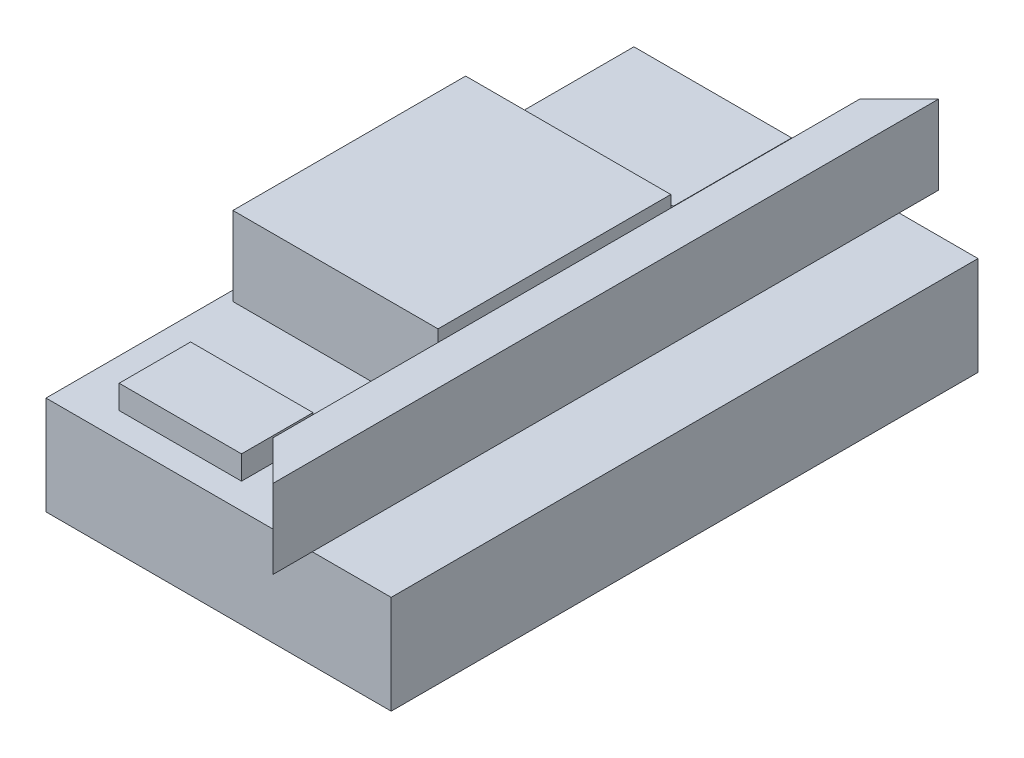
SolidWorks part; units mm, degrees
ref_plane "Front Plane" through (0, 0, 0) normal (0, 0, 1) x (1, 0, 0)
ref_plane "Top Plane" through (0, 0, 0) normal (0, 1, 0) x (1, 0, 0)
ref_plane "Right Plane" through (0, 0, 0) normal (1, 0, 0) x (0, 0, -1)
sketch "Sketch1" plane through (0, 0, 0) normal (0, 0, 1) x (1, 0, 0)
  line L1 (0, 0) -> (222.25, 0)
  line L2 (0, 0) -> (0, 63.5)
  line L3 (0, 63.5) -> (222.25, 63.5)
  line L4 (222.25, 0) -> (222.25, 63.5)
  dimension "D1" = 63.5
  dimension "D2" = 222.25
extrude "Boss-Extrude1" add sketch "Sketch1" along normal blind 377.825
sketch "Sketch2" plane through (0, 63.5, 0) normal (0, 1, 0) x (1, 0, 0)
  line L0 (222.25, -377.825) -> (222.25, 0) construction
  line L1 (171.45, -403.225) -> (146.05, -403.225)
  line L2 (171.45, -403.225) -> (171.45, 25.4)
  line L3 (171.45, 25.4) -> (146.05, 25.4)
  line L4 (146.05, -403.225) -> (146.05, 25.4)
  line L7 (222.25, -377.825) -> (0, -377.825) construction
  line L8 (222.25, 0) -> (0, 0) construction
  dimension "D1" = 25.4
  dimension "D2" = 50.8
  dimension "D3" = 25.4
  dimension "D4" = 25.4
extrude "Boss-Extrude2" add sketch "Sketch2" along normal blind 50.8
sketch "Sketch3" plane through (0, 63.5, 0) normal (0, 1, 0) x (1, 0, 0)
  line L0 (0, -377.825) -> (0, 0) construction
  line L1 (138.43, -113.9825) -> (6.35, -113.9825)
  line L2 (138.43, -113.9825) -> (138.43, -263.8425)
  line L3 (138.43, -263.8425) -> (6.35, -263.8425)
  line L4 (6.35, -113.9825) -> (6.35, -263.8425)
  line L5 (146.05, 0) -> (146.05, -377.825) construction
  point P8 (6.35, -188.9125)
  point P9 (0, -188.9125)
  dimension "D1" = 6.35
  dimension "D2" = 7.62
  dimension "D3" = 149.86
extrude "Boss-Extrude3" add sketch "Sketch3" along normal blind 50.8
sketch "Sketch4" plane through (0, 63.5, 0) normal (0, 1, 0) x (1, 0, 0)
  line L1 (120.4067, -94.2972) -> (18.8067, -94.2972)
  line L2 (120.4067, -94.2972) -> (120.4067, -18.0972)
  line L3 (120.4067, -18.0972) -> (18.8067, -18.0972)
  line L4 (18.8067, -94.2972) -> (18.8067, -18.0972)
  dimension "D1" = 101.6
  dimension "D2" = 76.2
extrude "Boss-Extrude4" add sketch "Sketch4" along normal blind 25.4
sketch "Sketch5" plane through (0, 63.5, 0) normal (0, 1, 0) x (1, 0, 0)
  line L1 (109.3033, -361.2493) -> (30.5246, -361.2493)
  line L2 (109.3033, -361.2493) -> (109.3033, -315.2336)
  line L3 (109.3033, -315.2336) -> (30.5246, -315.2336)
  line L4 (30.5246, -361.2493) -> (30.5246, -315.2336)
extrude "Boss-Extrude5" add sketch "Sketch5" along normal blind 15.24
sketch "Sketch8" plane through (0, 114.3, 0) normal (0, 1, 0) x (1, 0, 0)
  line L0 (171.45, 25.4) -> (146.05, 0)
  line L1 (146.05, 0) -> (146.05, 25.4)
  line L2 (146.05, 25.4) -> (171.45, 25.4)
  line L6 (171.45, -403.225) -> (146.05, -377.825)
  line L7 (146.05, 25.4) -> (146.05, -403.225) construction
  line L8 (171.45, -403.225) -> (146.05, -403.225)
  line L9 (146.05, -403.225) -> (146.05, -377.825)
  point P10 (146.05, -374.683)
extrude "Cut-Extrude1" cut sketch "Sketch8" against normal blind 127
